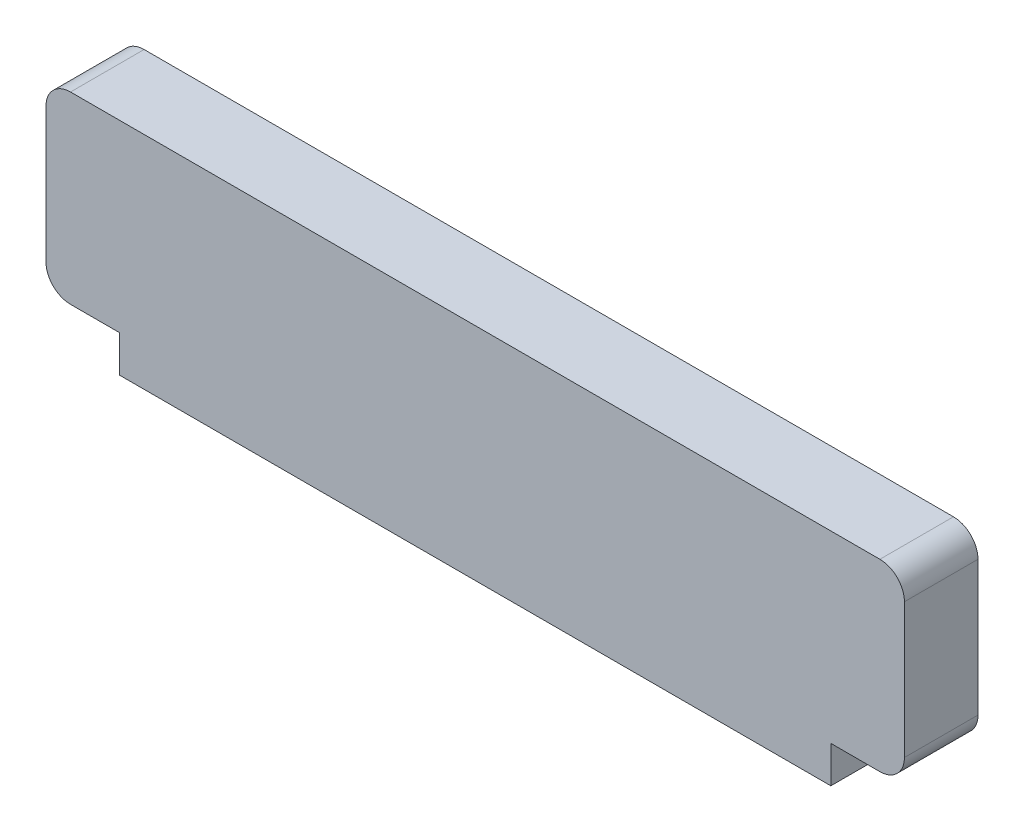
SolidWorks part; units mm, degrees
material "Стекло"
ref_plane "Спереди" through (0, 0, 0) normal (0, 0, 1) x (1, 0, 0)
ref_plane "Сверху" through (0, 0, 0) normal (0, 1, 0) x (1, 0, 0)
ref_plane "Справа" through (0, 0, 0) normal (1, 0, 0) x (0, 0, -1)
sketch "Эскиз1" plane through (0, 0, 0) normal (0, 0, 1) x (1, 0, 0)
  line L1 (0, 0) -> (70, 0)
  line L2 (0, 0) -> (0, 15)
  line L3 (0, 15) -> (70, 15)
  line L4 (70, 0) -> (70, 15)
  dimension "D1" = 70
  dimension "D2" = 15
extrude "Бобышка-Вытянуть1" add sketch "Эскиз1" along normal blind 6
fillet "Скругление1" radius 2 4 edges at (0, 15, 3) (0, 0, 3) (70, 0, 3) (70, 15, 3)
sketch "Эскиз2" plane through (0, 0, 0) normal (0, -1, 0) x (1, 0, 0)
  line L0 (2, 6) -> (68, 6) construction
  line L1 (6, 6) -> (64, 6)
  line L2 (6, 6) -> (6, 0)
  line L3 (64, 0) -> (6, 0)
  line L4 (68, 0) -> (68, 8.9386) construction
  line L6 (68, 0) -> (68, 6) construction
  line L7 (35, 6) -> (35, -12.1934) construction
  line L8 (2, 0) -> (2, 10.021) construction
  line L9 (64, 6) -> (64, 0)
  line L10 (2, 0) -> (68, 0) construction
  dimension "D1" = 6
  dimension "D2" = 4
  dimension "D3" = 4
extrude "Бобышка-Вытянуть2" add sketch "Эскиз2" along normal blind 3
